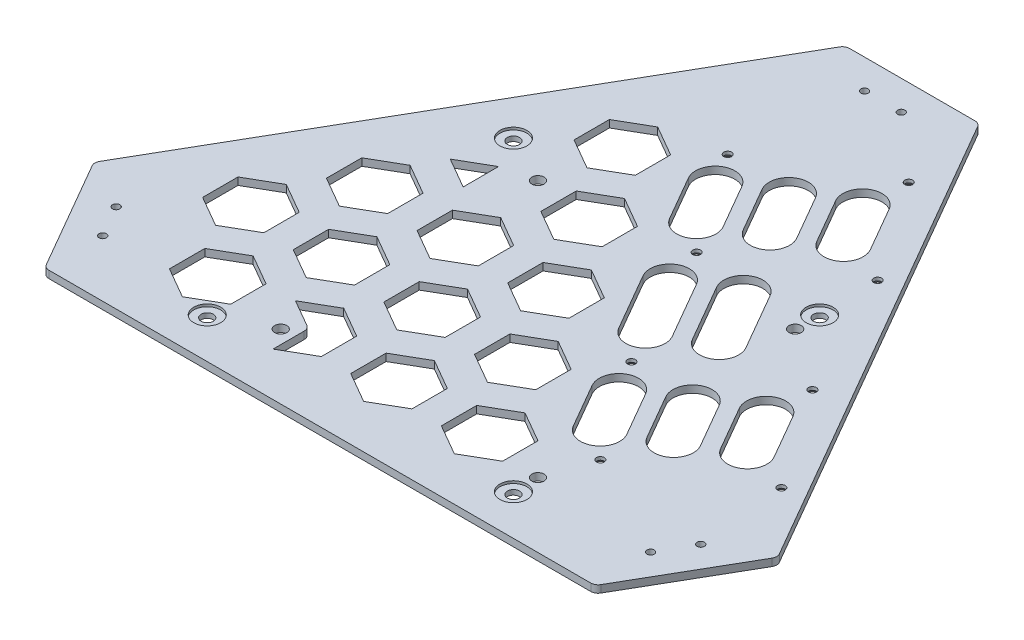
SolidWorks part; units mm, degrees
ref_plane "前基準面" through (0, 0, 0) normal (0, 0, 1) x (1, 0, 0)
ref_plane "上基準面" through (0, 0, 0) normal (0, 1, 0) x (1, 0, 0)
ref_plane "右基準面" through (0, 0, 0) normal (1, 0, 0) x (0, 0, -1)
ref_plane "平面1" through (0, -3, 0) normal (0, -1, 0) x (1, 0, 0)
sketch "草圖1" plane through (0, -3, 0) normal (0, -1, 0) x (1, 0, 0)
  line L0 (-138.7528, 47.5748) -> (-28.1754, -143.9508)
  line L1 (-25.5774, -145.4508) -> (25.5774, -145.4508)
  line L2 (28.1754, -143.9508) -> (138.7528, 47.5748)
  line L3 (138.7528, 50.5748) -> (113.1754, 94.876)
  line L4 (110.5774, 96.376) -> (-110.5774, 96.376)
  line L5 (-113.1754, 94.876) -> (-138.7528, 50.5748)
  arc A0 (-28.1754, -143.9508) -> (-25.5774, -145.4508) centre (-25.5774, -142.4508) ccw
  arc A1 (25.5774, -145.4508) -> (28.1754, -143.9508) centre (25.5774, -142.4508) ccw
  arc A2 (138.7528, 47.5748) -> (138.7528, 50.5748) centre (136.1547, 49.0748) ccw
  arc A3 (113.1754, 94.876) -> (110.5774, 96.376) centre (110.5774, 93.376) ccw
  arc A4 (-110.5774, 96.376) -> (-113.1754, 94.876) centre (-110.5774, 93.376) ccw
  arc A5 (-138.7528, 50.5748) -> (-138.7528, 47.5748) centre (-136.1547, 49.0748) ccw
extrude "填料-伸長1" add sketch "草圖1" against normal blind 3
sketch "草圖2" plane through (0, -3, 0) normal (0, -1, 0) x (1, 0, 0)
  line L0 (39.2497, -96.7695) -> (49.7497, -78.583)
  line L1 (35.8933, -70.583) -> (25.3933, -88.7695)
  arc A0 (49.7497, -78.583) -> (35.8933, -70.583) centre (42.8215, -74.583) ccw
  arc A1 (25.3933, -88.7695) -> (39.2497, -96.7695) centre (32.3215, -92.7695) ccw
extrude "除料-伸長1" cut sketch "草圖2" against normal through all
sketch "草圖3" plane through (0, -3, 0) normal (0, -1, 0) x (1, 0, 0)
  line L0 (-49.5, -71.2969) -> (-37, -78.5138)
  line L1 (-37, -78.5138) -> (-24.5, -71.2969)
  line L2 (-24.5, -71.2969) -> (-24.5, -56.8631)
  line L3 (-24.5, -56.8631) -> (-37, -49.6462)
  line L4 (-37, -49.6462) -> (-49.5, -56.8631)
  line L5 (-49.5, -56.8631) -> (-49.5, -71.2969)
extrude "除料-伸長2" cut sketch "草圖3" against normal through all
sketch "草圖4" plane through (0, -3, 0) normal (0, -1, 0) x (1, 0, 0)
  line L0 (92.9297, -3.793) -> (103.4297, 14.3935)
  line L1 (89.5733, 22.3935) -> (79.0733, 4.207)
  arc A0 (103.4297, 14.3935) -> (89.5733, 22.3935) centre (96.5015, 18.3935) ccw
  arc A1 (79.0733, 4.207) -> (92.9297, -3.793) centre (86.0015, 0.207) ccw
extrude "除料-伸長3" cut sketch "草圖4" against normal through all
sketch "草圖5" plane through (0, -3, 0) normal (0, -1, 0) x (1, 0, 0)
  line L0 (73.8772, 7.207) -> (84.3772, 25.3935)
  line L1 (70.5208, 33.3935) -> (60.0208, 15.207)
  arc A0 (60.0208, 15.207) -> (73.8772, 7.207) centre (66.949, 11.207) ccw
  arc A1 (84.3772, 25.3935) -> (70.5208, 33.3935) centre (77.449, 29.3935) ccw
extrude "除料-伸長4" cut sketch "草圖5" against normal through all
sketch "草圖6" plane through (0, -3, 0) normal (0, -1, 0) x (1, 0, 0)
  line L0 (45.5372, -41.8794) -> (59.0372, -18.4967)
  line L1 (45.1808, -10.4967) -> (31.6808, -33.8794)
  arc A0 (59.0372, -18.4967) -> (45.1808, -10.4967) centre (52.109, -14.4967) ccw
  arc A1 (31.6808, -33.8794) -> (45.5372, -41.8794) centre (38.609, -37.8794) ccw
extrude "除料-伸長5" cut sketch "草圖6" against normal through all
sketch "草圖7" plane through (0, -3, 0) normal (0, -1, 0) x (1, 0, 0)
  line L0 (26.4846, -30.8794) -> (39.9846, -7.4967)
  line L1 (26.1282, 0.5033) -> (12.6282, -22.8794)
  arc A0 (39.9846, -7.4967) -> (26.1282, 0.5033) centre (33.0564, -3.4967) ccw
  arc A1 (12.6282, -22.8794) -> (26.4846, -30.8794) centre (19.5564, -26.8794) ccw
extrude "除料-伸長6" cut sketch "草圖7" against normal through all
sketch "草圖8" plane through (0, -3, 0) normal (0, -1, 0) x (1, 0, 0)
  line L0 (54.8246, 18.207) -> (65.3246, 36.3935)
  line L1 (51.4682, 44.3935) -> (40.9682, 26.207)
  arc A0 (40.9682, 26.207) -> (54.8246, 18.207) centre (47.8964, 22.207) ccw
  arc A1 (65.3246, 36.3935) -> (51.4682, 44.3935) centre (58.3964, 40.3935) ccw
extrude "除料-伸長7" cut sketch "草圖8" against normal through all
sketch "草圖9" plane through (0, -3, 0) normal (0, -1, 0) x (1, 0, 0)
  line L0 (-12.5, -7.2169) -> (0, -14.4338)
  line L1 (0, -14.4338) -> (12.5, -7.2169)
  line L2 (12.5, -7.2169) -> (12.5, 7.2169)
  line L3 (12.5, 7.2169) -> (0, 14.4338)
  line L4 (0, 14.4338) -> (-12.5, 7.2169)
  line L5 (-12.5, 7.2169) -> (-12.5, -7.2169)
extrude "除料-伸長8" cut sketch "草圖9" against normal through all
sketch "草圖10" plane through (0, -3, 0) normal (0, -1, 0) x (1, 0, 0)
  line L0 (-49.5, -7.2169) -> (-37, -14.4338)
  line L1 (-37, -14.4338) -> (-24.5, -7.2169)
  line L2 (-24.5, -7.2169) -> (-24.5, 7.2169)
  line L3 (-24.5, 7.2169) -> (-37, 14.4338)
  line L4 (-37, 14.4338) -> (-49.5, 7.2169)
  line L5 (-49.5, 7.2169) -> (-49.5, -7.2169)
extrude "除料-伸長9" cut sketch "草圖10" against normal through all
sketch "草圖11" plane through (0, -3, 0) normal (0, -1, 0) x (1, 0, 0)
  line L0 (-86.5, -7.2169) -> (-74, -14.4338)
  line L1 (-74, -14.4338) -> (-61.5, -7.2169)
  line L2 (-61.5, -7.2169) -> (-61.5, 7.2169)
  line L3 (-61.5, 7.2169) -> (-74, 14.4338)
  line L4 (-74, 14.4338) -> (-86.5, 7.2169)
  line L5 (-86.5, 7.2169) -> (-86.5, -7.2169)
extrude "除料-伸長10" cut sketch "草圖11" against normal through all
sketch "草圖12" plane through (0, -3, 0) normal (0, -1, 0) x (1, 0, 0)
  line L0 (-18.5, -46.4708) -> (-6, -39.2539)
  line L1 (-6, -39.2539) -> (-6, -24.8202)
  line L2 (-6, -24.8202) -> (-18.5, -17.6033)
  line L3 (-18.5, -17.6033) -> (-31, -24.8202)
  line L4 (-31, -24.8202) -> (-31, -39.2539)
  line L5 (-31, -39.2539) -> (-18.5, -46.4708)
extrude "除料-伸長11" cut sketch "草圖12" against normal through all
sketch "草圖13" plane through (0, -3, 0) normal (0, -1, 0) x (1, 0, 0)
  line L0 (18.5, 17.6092) -> (31, 24.8261)
  line L1 (31, 24.8261) -> (31, 39.2598)
  line L2 (31, 39.2598) -> (18.5, 46.4767)
  line L3 (18.5, 46.4767) -> (6, 39.2598)
  line L4 (6, 39.2598) -> (6, 24.8261)
  line L5 (6, 24.8261) -> (18.5, 17.6092)
extrude "除料-伸長12" cut sketch "草圖13" against normal through all
sketch "草圖14" plane through (0, -3, 0) normal (0, -1, 0) x (1, 0, 0)
  line L0 (-18.5, 17.6092) -> (-6, 24.8261)
  line L1 (-6, 24.8261) -> (-6, 39.2598)
  line L2 (-6, 39.2598) -> (-18.5, 46.4767)
  line L3 (-18.5, 46.4767) -> (-31, 39.2598)
  line L4 (-31, 39.2598) -> (-31, 24.8261)
  line L5 (-31, 24.8261) -> (-18.5, 17.6092)
extrude "除料-伸長13" cut sketch "草圖14" against normal through all
sketch "草圖15" plane through (0, -3, 0) normal (0, -1, 0) x (1, 0, 0)
  line L0 (-55.5, 17.6092) -> (-43, 24.8261)
  line L1 (-43, 24.8261) -> (-43, 39.2598)
  line L2 (-43, 39.2598) -> (-55.5, 46.4767)
  line L3 (-55.5, 46.4767) -> (-68, 39.2598)
  line L4 (-68, 39.2598) -> (-68, 24.8261)
  line L5 (-68, 24.8261) -> (-55.5, 17.6092)
extrude "除料-伸長14" cut sketch "草圖15" against normal through all
sketch "草圖16" plane through (0, -3, 0) normal (0, -1, 0) x (1, 0, 0)
  line L0 (-92.5, 17.6092) -> (-80, 24.8261)
  line L1 (-80, 24.8261) -> (-80, 39.2598)
  line L2 (-80, 39.2598) -> (-92.5, 46.4767)
  line L3 (-92.5, 46.4767) -> (-105, 39.2598)
  line L4 (-105, 39.2598) -> (-105, 24.8261)
  line L5 (-105, 24.8261) -> (-92.5, 17.6092)
extrude "除料-伸長15" cut sketch "草圖16" against normal through all
sketch "草圖17" plane through (0, -3, 0) normal (0, -1, 0) x (1, 0, 0)
  line L0 (-74, 49.6462) -> (-61.5, 56.8631)
  line L1 (-61.5, 56.8631) -> (-61.5, 71.2969)
  line L2 (-61.5, 71.2969) -> (-74, 78.5138)
  line L3 (-74, 78.5138) -> (-86.5, 71.2969)
  line L4 (-86.5, 71.2969) -> (-86.5, 56.8631)
  line L5 (-86.5, 56.8631) -> (-74, 49.6462)
extrude "除料-伸長16" cut sketch "草圖17" against normal through all
sketch "草圖18" plane through (0, -3, 0) normal (0, -1, 0) x (1, 0, 0)
  line L0 (-49.5, 56.8631) -> (-37, 49.6462)
  line L1 (-37, 49.6462) -> (-24.5, 56.8631)
  line L2 (-24.5, 56.8631) -> (-24.5, 71.2969)
  line L3 (-24.5, 71.2969) -> (-37, 78.5138)
  line L4 (-37, 78.5138) -> (-37, 65.8121)
  line L5 (-38.5, 63.214) -> (-49.5, 56.8631)
  arc A0 (-37, 65.8121) -> (-38.5, 63.214) centre (-40, 65.8121) cw
extrude "除料-伸長17" cut sketch "草圖18" against normal through all
sketch "草圖19" plane through (0, -3, 0) normal (0, -1, 0) x (1, 0, 0)
  line L0 (-12.5, 56.8631) -> (0, 49.6462)
  line L1 (0, 49.6462) -> (12.5, 56.8631)
  line L2 (12.5, 56.8631) -> (12.5, 71.2969)
  line L3 (12.5, 71.2969) -> (0, 78.5138)
  line L4 (0, 78.5138) -> (-12.5, 71.2969)
  line L5 (-12.5, 71.2969) -> (-12.5, 56.8631)
extrude "除料-伸長18" cut sketch "草圖19" against normal through all
sketch "草圖20" plane through (0, -3, 0) normal (0, -1, 0) x (1, 0, 0)
  line L0 (24.5, 56.8631) -> (37, 49.6462)
  line L1 (37, 49.6462) -> (49.5, 56.8631)
  line L2 (49.5, 56.8631) -> (49.5, 71.2969)
  line L3 (49.5, 71.2969) -> (37, 78.5138)
  line L4 (37, 78.5138) -> (24.5, 71.2969)
  line L5 (24.5, 71.2969) -> (24.5, 56.8631)
extrude "除料-伸長19" cut sketch "草圖20" against normal through all
sketch "草圖21" plane through (0, -3, 0) normal (0, -1, 0) x (1, 0, 0)
  line L0 (20.1972, -85.7695) -> (30.6972, -67.583)
  line L1 (16.8408, -59.583) -> (6.3408, -77.7695)
  arc A0 (30.6972, -67.583) -> (16.8408, -59.583) centre (23.769, -63.583) ccw
  arc A1 (6.3408, -77.7695) -> (20.1972, -85.7695) centre (13.269, -81.7695) ccw
extrude "除料-伸長20" cut sketch "草圖21" against normal through all
sketch "草圖22" plane through (0, -3, 0) normal (0, -1, 0) x (1, 0, 0)
  line L0 (1.1446, -74.7695) -> (11.6446, -56.583)
  line L1 (-2.2118, -48.583) -> (-12.7118, -66.7695)
  arc A0 (11.6446, -56.583) -> (-2.2118, -48.583) centre (4.7164, -52.583) ccw
  arc A1 (-12.7118, -66.7695) -> (1.1446, -74.7695) centre (-5.7836, -70.7695) ccw
extrude "除料-伸長21" cut sketch "草圖22" against normal through all
sketch "草圖23" plane through (0, 0, 0) normal (0, 1, 0) x (-1, 0, 0)
  line L0 (68, -24.8202) -> (55.5, -17.6033)
  line L1 (55.5, -17.6033) -> (55.5, -32.0371)
  line L2 (55.5, -32.0371) -> (68, -24.8202)
extrude "除料-伸長22" cut sketch "草圖23" against normal through all
hole_wizard "M3 平頭機械螺釘的錐孔1" positions "草圖25" profile "草圖24" countersink size "M3" standard "Ansi Metric"
sketch "草圖25" plane through (0, -3, 0) normal (0, -1, 0) x (-1, 0, 0)
  point P0 (-68.9339, -50.845)
  point P1 (-115.7859, -23.795)
  point P2 (-40.6498, -9.8555)
  point P3 (-87.5018, 17.1945)
  point P4 (-15.2539, 42.1315)
  point P5 (-62.1059, 69.1815)
  point P6 (13.0302, 83.121)
  point P7 (-33.8218, 110.171)
sketch "草圖24" plane through (68.9339, -3, 50.845) normal (1, 0, 0) x (0, 0, -1)
  line L0 (0, 0) -> (0, 3)
  line L1 (0, 3) -> (1.6, 3)
  line L2 (1.6, 3) -> (1.6, 1.7)
  line L3 (1.6, 1.7) -> (3.3, 0)
  line L5 (3.3, 0) -> (0, 0)
  line L6 (-1.6, 1.7) -> (-3.3, 0) construction
  line L11 (0, -6.35) -> (0, 107.95) construction
  dimension "砮 ふ 畖" = 3.2
  dimension "砮 ふ瞏 " = 3
  dimension " 狠繞ふ 畖" = 6.6
  dimension " 狠繞ふà " = 90
hole_wizard "鑽孔1" positions "草圖27" profile "草圖26" legacy
sketch "草圖27" plane through (0, 0, 0) normal (0, 1, 0) x (1, 0, 0)
  point P0 (62.5, 45.124)
  point P1 (-62.5, -79.876)
  point P2 (62.5, -79.876)
  point P3 (-62.5, 45.124)
sketch "草圖26" plane through (62.5, 0, -45.124) normal (1, 0, 0) x (0, 0, 1)
  line L0 (0, 0) -> (0, 3)
  line L1 (0, 3) -> (2.5, 3)
  line L2 (2.5, 3) -> (2.5, 1)
  line L3 (2.5, 1) -> (5.5, 1)
  line L4 (5.5, 1) -> (5.5, 0)
  line L5 (5.5, 0) -> (0, 0)
  line L6 (0, 110) -> (0, -10) construction
  dimension " 畖" = 5
  dimension "瞏 " = 3
  dimension "琖ふ 畖1" = 11
  dimension "琖ふ瞏 1" = 1
hole_wizard "Ø3.0 (3) 直徑孔1" positions "草圖29" profile "草圖28" hole size "Ø3.0" standard "Ansi Metric"
sketch "草圖29" plane through (0, 0, 0) normal (0, 1, 0) x (1, 0, 0)
  point P0 (-119.3218, -60.2302)
  point P1 (-111.8218, -73.2206)
  point P2 (7.5, 133.4508)
  point P3 (-7.5, 133.4508)
  point P4 (119.3218, -60.2302)
  point P5 (111.8218, -73.2206)
sketch "草圖28" plane through (-119.3218, 0, 60.2302) normal (1, 0, 0) x (0, 0, 1)
  line L0 (0, 0) -> (0, 3)
  line L1 (0, 3) -> (1.5, 3)
  line L2 (1.5, 3) -> (1.5, 0)
  line L5 (1.5, 0) -> (0, 0)
  line L11 (0, -6.35) -> (0, 107.95) construction
  dimension "砮 ふ 畖" = 3
  dimension "砮 ふ瞏 " = 3
hole_wizard "Ø5.0 (5) 直徑孔1" positions "草圖31" profile "草圖30" hole size "Ø5.0" standard "Ansi Metric"
sketch "草圖31" plane through (0, 0, 0) normal (0, 1, 0) x (1, 0, 0)
  point P0 (-42.5, 35.124)
  point P1 (62.5, 35.124)
  point P2 (62.5, -69.876)
  point P3 (-42.5, -69.876)
sketch "草圖30" plane through (-42.5, 0, -35.124) normal (1, 0, 0) x (0, 0, 1)
  line L0 (0, 0) -> (0, 3)
  line L1 (0, 3) -> (2.5, 3)
  line L2 (2.5, 3) -> (2.5, 0)
  line L5 (2.5, 0) -> (0, 0)
  line L11 (0, -6.35) -> (0, 107.95) construction
  dimension "砮 ふ 畖" = 5
  dimension "砮 ふ瞏 " = 3
